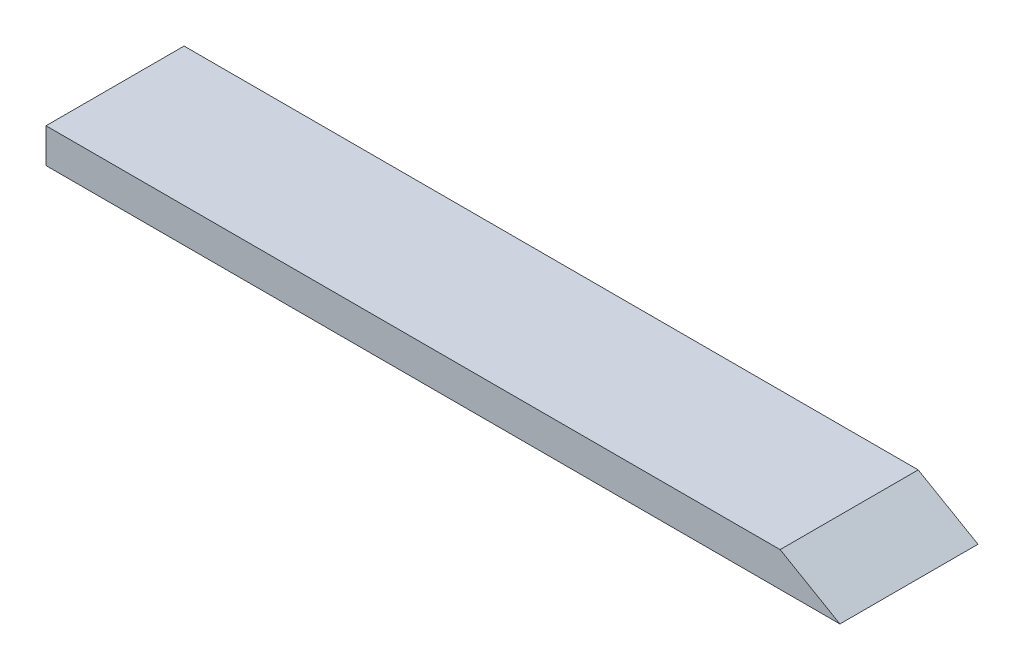
SolidWorks part; units mm, degrees
ref_plane "Front Plane" through (0, 0, 0) normal (0, 0, 1) x (1, 0, 0)
ref_plane "Top Plane" through (0, 0, 0) normal (0, 1, 0) x (1, 0, 0)
ref_plane "Right Plane" through (0, 0, 0) normal (1, 0, 0) x (0, 0, -1)
sketch "Sketch1" plane through (0, 0, 0) normal (0, 1, 0) x (1, 0, 0)
  line L1 (-57.5, -10) -> (57.5, -10)
  line L2 (-57.5, -10) -> (-57.5, 10)
  line L3 (-57.5, 10) -> (57.5, 10)
  line L4 (57.5, -10) -> (57.5, 10)
  line L5 (-57.5, -10) -> (57.5, 10) construction
  line L6 (-57.5, 10) -> (57.5, -10) construction
  point P0 (0, 0)
  dimension "D1" = 20
  dimension "D2" = 115
extrude "Boss-Extrude1" add sketch "Sketch1" along normal blind 5
sketch "Sketch2" plane through (0, 0, 10) normal (0, 0, 1) x (1, 0, 0)
  line L0 (57.5, 0) -> (48.8397, 5)
  line L1 (-57.5, 5) -> (57.5, 5) construction
  line L2 (-57.5, 0) -> (57.5, 0) construction
  line L3 (48.8397, 5) -> (57.5, 5)
  line L4 (57.5, 5) -> (57.5, 0)
  dimension "D1" = 30
extrude "Cut-Extrude1" cut sketch "Sketch2" against normal through all
